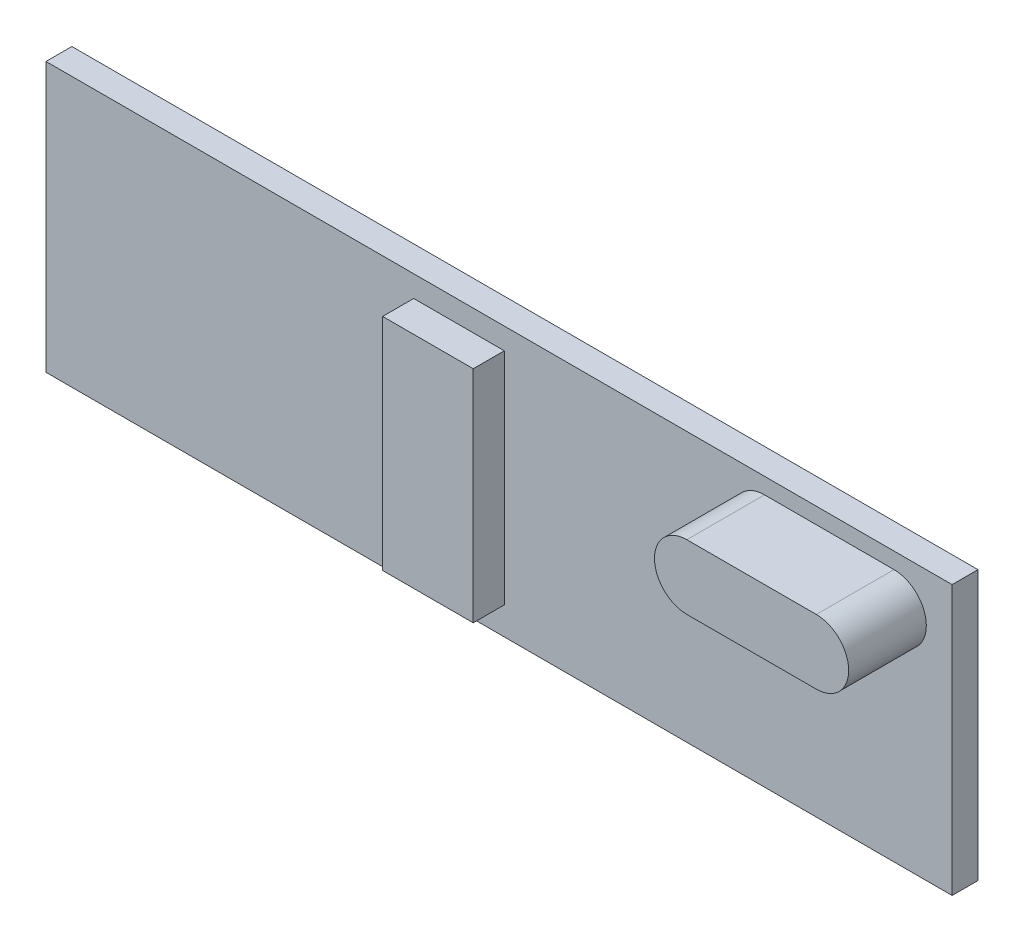
SolidWorks part; units mm, degrees
ref_plane "Front Plane" through (0, 0, 0) normal (0, 0, 1) x (1, 0, 0)
ref_plane "Top Plane" through (0, 0, 0) normal (0, 1, 0) x (1, 0, 0)
ref_plane "Right Plane" through (0, 0, 0) normal (1, 0, 0) x (0, 0, -1)
sketch "Sketch1" plane through (0, 0, 0) normal (0, 0, 1) x (1, 0, 0)
  line L1 (17.5, -5.2) -> (-17.5, -5.2)
  line L2 (17.5, -5.2) -> (17.5, 5.2)
  line L3 (17.5, 5.2) -> (-17.5, 5.2)
  line L4 (-17.5, -5.2) -> (-17.5, 5.2)
  line L5 (17.5, -5.2) -> (-17.5, 5.2) construction
  line L6 (17.5, 5.2) -> (-17.5, -5.2) construction
  point P0 (0, 0)
  dimension "D1" = 10.4
  dimension "D2" = 35
extrude "Boss-Extrude1" add sketch "Sketch1" along normal blind 1
sketch "Sketch2" plane through (0, 0, 1) normal (0, 0, 1) x (1, 0, 0)
  line L0 (15.2539, 3.329) -> (10.2539, 3.329) construction
  line L1 (15.2539, 2.079) -> (10.2539, 2.079)
  line L2 (15.2539, 4.579) -> (10.2539, 4.579)
  line L4 (1.0043, -3.9986) -> (-2.4957, -3.9986)
  line L5 (1.0043, -3.9986) -> (1.0043, 4.5014)
  line L6 (1.0043, 4.5014) -> (-2.4957, 4.5014)
  line L7 (-2.4957, -3.9986) -> (-2.4957, 4.5014)
  line L8 (1.0043, -3.9986) -> (-2.4957, 4.5014) construction
  line L9 (1.0043, 4.5014) -> (-2.4957, -3.9986) construction
  arc A0 (15.2539, 2.079) -> (15.2539, 4.579) centre (15.2539, 3.329) ccw
  arc A1 (10.2539, 4.579) -> (10.2539, 2.079) centre (10.2539, 3.329) ccw
  point P2 (12.7539, 3.329)
  point P7 (-0.7457, 0.2514)
  point P12 (0.4835, -0.7997)
  point P13 (0.4092, -0.9857)
  dimension "D1" = 5
  dimension "D2" = 2.5
  dimension "D3" = 8.5
  dimension "D4" = 3.5
extrude "Boss-Extrude3" add sketch "Sketch2" along normal blind 3 contours L2 A1 L1 A0
sketch "Sketch3" plane through (0, 0, 1) normal (0, 0, 1) x (1, 0, 0)
  line L1 (-3.2972, 4.3726) -> (0.2028, 4.3726)
  line L2 (-3.2972, 4.3726) -> (-3.2972, -4.1274)
  line L3 (-3.2972, -4.1274) -> (0.2028, -4.1274)
  line L4 (0.2028, 4.3726) -> (0.2028, -4.1274)
  point P4 (0.9671, -4.4672)
  dimension "D1" = 8.5
  dimension "D2" = 3.5
extrude "Boss-Extrude4" add sketch "Sketch3" along normal blind 1.2
